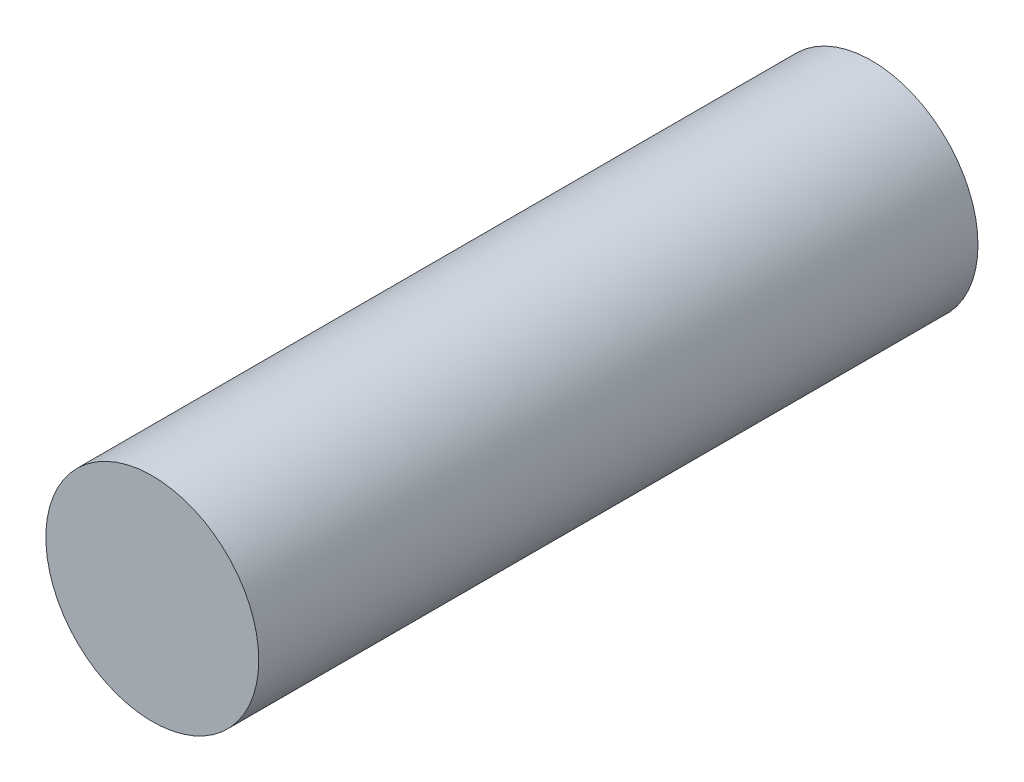
SolidWorks part; units mm, degrees
ref_plane "Front" through (0, 0, 0) normal (0, 0, 1) x (1, 0, 0)
ref_plane "Top" through (0, 0, 0) normal (0, 1, 0) x (1, 0, 0)
ref_plane "Right" through (0, 0, 0) normal (1, 0, 0) x (0, 0, -1)
sketch "Sketch1" plane through (0, 0, 0) normal (0, 0, 1) x (1, 0, 0)
  circle A0 centre (0, 0) radius 7.4
  dimension "D1" = 14.8
extrude "Boss-Extrude1" add sketch "Sketch1" along normal mid plane 50
